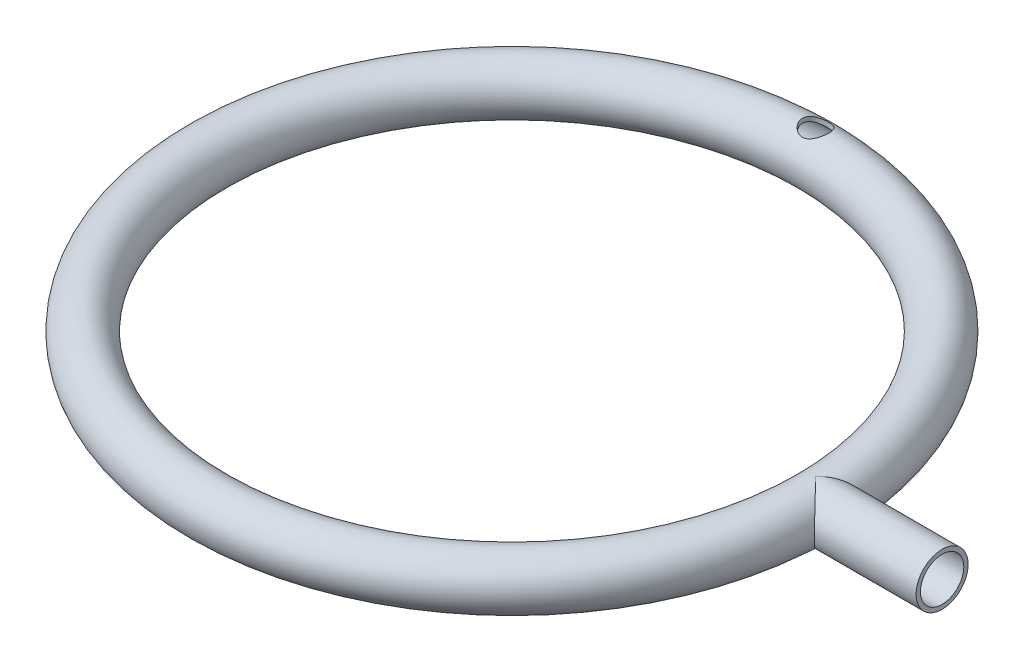
SolidWorks part; units mm, degrees
ref_plane "Front Plane" through (0, 0, 0) normal (0, 0, 1) x (1, 0, 0)
ref_plane "Top Plane" through (0, 0, 0) normal (0, 1, 0) x (1, 0, 0)
ref_plane "Right Plane" through (0, 0, 0) normal (1, 0, 0) x (0, 0, -1)
sketch "Sketch1" plane through (0, 0, 0) normal (0, 0, 1) x (1, 0, 0)
  line L0 (0, 0) -> (0, 10.2449) construction
  circle A0 centre (-44.45, 0) radius 3.175
  circle A1 centre (-44.45, 0) radius 3.81
  dimension "D1" = 6.35
  dimension "D2" = 44.45
  dimension "D3" = 7.62
revolve "Revolve1" add sketch "Sketch1" angle 360 about L0
ref_plane "Plane1" through (44.45, 0, 0) normal (1, 0, 0) x (0, 0, -1)
sketch "Sketch3" plane through (44.45, 0, 0) normal (1, 0, 0) x (0, 0, -1)
  circle A0 centre (0, 0) radius 3.175
  circle A1 centre (0, 0) radius 3.81
  dimension "D1" = 6.35
  dimension "D2" = 7.62
extrude "Boss-Extrude1" add sketch "Sketch3" along normal blind 18.542
sketch "Sketch4" plane through (44.45, 0, 0) normal (1, 0, 0) x (0, 0, -1)
  circle A0 centre (0, 0) radius 3.175
extrude "Cut-Extrude5" cut sketch "Sketch4" along normal blind 12.7
sketch "Sketch5" plane through (0, 0, 0) normal (0, 1, 0) x (1, 0, 0)
  circle A0 centre (0, 44.45) radius 1.905
  dimension "D1" = 3.81
  dimension "D2" = 44.45
extrude "Cut-Extrude6" cut sketch "Sketch5" along normal blind 12.7
sketch "Sketch6" plane through (0, 0, 0) normal (0, 1, 0) x (1, 0, 0)
  circle A0 centre (0, 0) radius 40.64 construction
